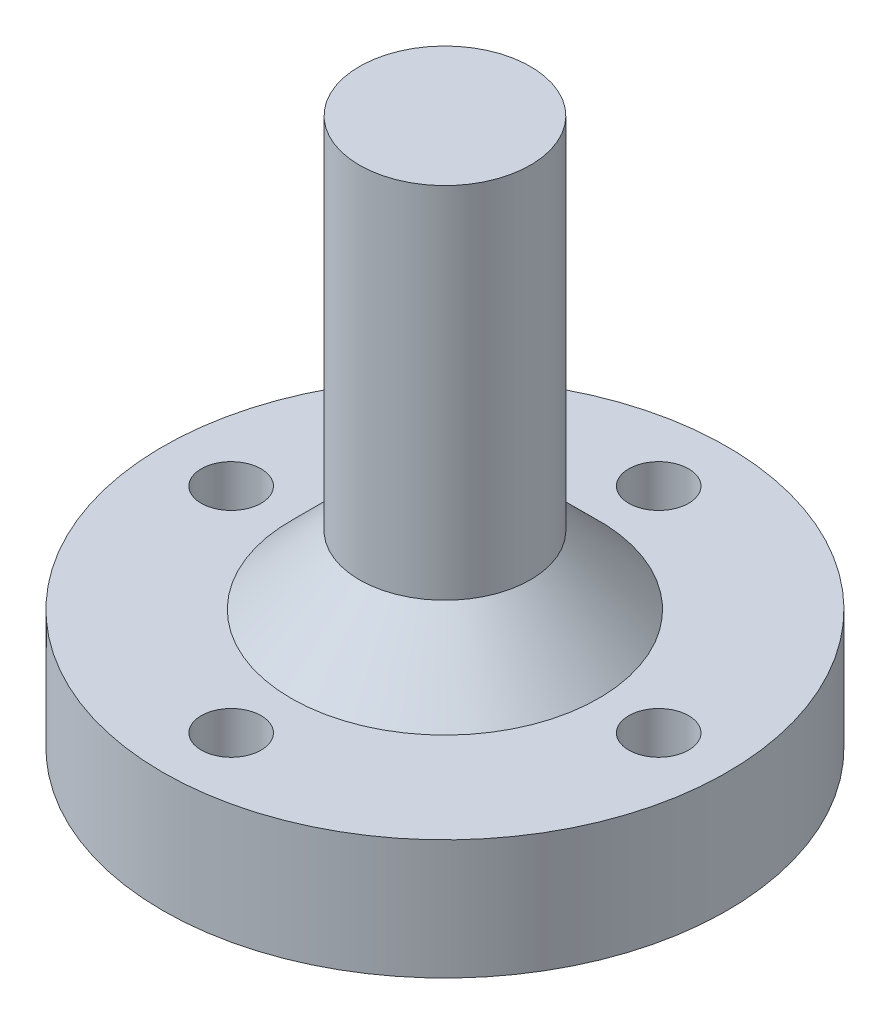
SolidWorks part; units mm, degrees
ref_plane "Front Plane" through (0, 0, 0) normal (0, 0, 1) x (1, 0, 0)
ref_plane "Top Plane" through (0, 0, 0) normal (0, 1, 0) x (1, 0, 0)
ref_plane "Right Plane" through (0, 0, 0) normal (1, 0, 0) x (0, 0, -1)
sketch "Sketch1" plane through (0, 0, 0) normal (0, 1, 0) x (1, 0, 0)
  circle A0 centre (0, 0) radius 16.5
  dimension "D1" = 33
extrude "Boss-Extrude1" add sketch "Sketch1" along normal blind 7
sketch "Sketch2" plane through (0, 7, 0) normal (0, 1, 0) x (1, 0, 0)
  circle A0 centre (0, 0) radius 12.5 construction
  circle A1 centre (0, 12.5) radius 1.75
  dimension "D1" = 25
  dimension "D2" = 3.5
extrude "Cut-Extrude1" cut sketch "Sketch2" against normal through all
pattern_circular "CirPattern1" count 4 over 360 about axis through (0, 0, 0) along (0, 1, 0) of "Cut-Extrude1"
sketch "Sketch3" plane through (0, 7, 0) normal (0, 1, 0) x (1, 0, 0)
  circle A0 centre (0, 0) radius 5
  dimension "D1" = 10
extrude "Boss-Extrude2" add sketch "Sketch3" along normal blind 25
chamfer "Chamfer1" distance 4 angle 45 1 edges at (0, 7, 5)
sketch "Sketch6" plane through (0, 0, 0) normal (0, -1, 0) x (1, 0, 0)
  circle A0 centre (0, 0) radius 5.25
  dimension "D1" = 10.5
extrude "Cut-Extrude4" cut sketch "Sketch6" against normal blind 5.5
sketch "Sketch8" plane through (0, 5.5, 0) normal (0, -1, 0) x (1, 0, 0)
  circle A0 centre (0, 0) radius 2.75
  dimension "D1" = 5.5
extrude "Cut-Extrude5" cut sketch "Sketch8" against normal blind 6
